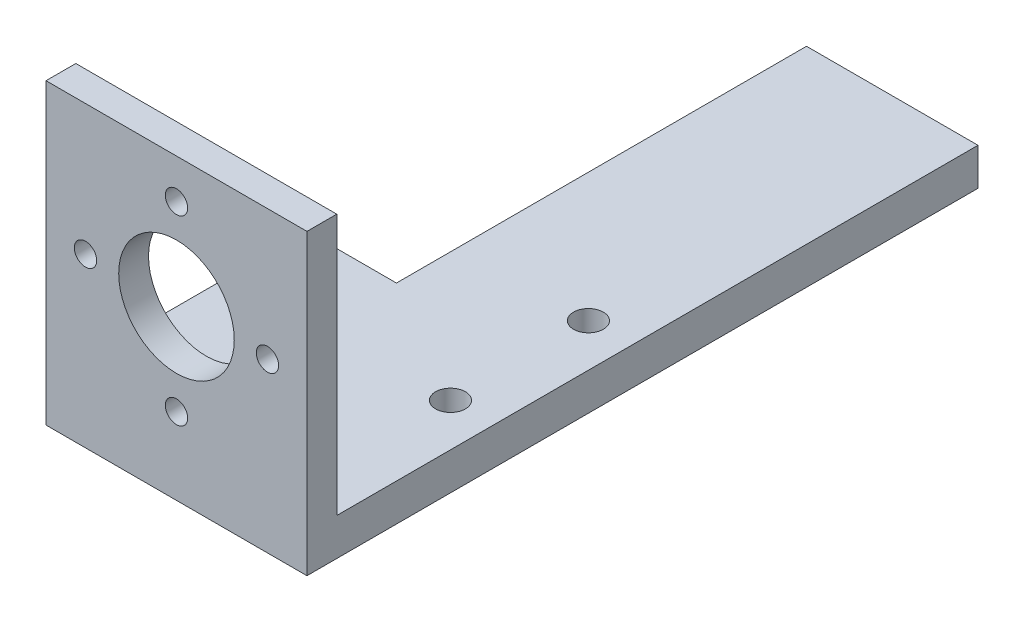
SolidWorks part; units mm, degrees
ref_plane "Front Plane" through (0, 0, 0) normal (0, 0, 1) x (1, 0, 0)
ref_plane "Top Plane" through (0, 0, 0) normal (0, 1, 0) x (1, 0, 0)
ref_plane "Right Plane" through (0, 0, 0) normal (1, 0, 0) x (0, 0, -1)
sketch "Sketch1" plane through (0, 0, 0) normal (0, 1, 0) x (1, 0, 0)
  line L0 (-17.5, 45) -> (17.5, 45)
  line L1 (17.5, 45) -> (17.5, -45)
  line L2 (17.5, -45) -> (-17.5, -45)
  line L3 (-17.5, -45) -> (-17.5, 45)
  line L4 (-11.75, -20) -> (11.75, -20)
  line L5 (-17.5, -10) -> (-5.5, -10)
  line L6 (-5.5, -10) -> (-5.5, 45)
  circle A0 centre (-11.75, -20) radius 2
  circle A1 centre (11.75, -20) radius 2
  circle A2 centre (11.75, -1.5) radius 2
  point P2 (-17.5, 0)
  point P5 (0, -45)
  point P9 (0, -20)
  point P14 (0, 0)
  dimension "D4" = 4
  dimension "D1" = 35
  dimension "D2" = 90
  dimension "D3" = 23.5
  dimension "D5" = 18.5
  dimension "D6" = 25
  dimension "D7" = 35
  dimension "D8" = 12
extrude "Boss-Extrude1" add sketch "Sketch1" along normal mid plane 5
sketch "Sketch2" plane through (0, 2.5, 0) normal (0, 1, 0) x (1, 0, 0)
  line L0 (-17.5, -45) -> (17.5, -45)
  line L1 (17.5, -45) -> (17.5, -41)
  line L2 (17.5, 45) -> (17.5, -45) construction
  line L3 (17.5, -41) -> (-17.5, -41)
  line L4 (-17.5, -45) -> (-17.5, -10) construction
  line L5 (-17.5, -41) -> (-17.5, -45)
  dimension "D1" = 4
extrude "Boss-Extrude2" add sketch "Sketch2" along normal blind 35
sketch "Sketch3" plane through (0, 0, 41) normal (0, 0, -1) x (-1, 0, 0)
  line L0 (0, 7.8) -> (0, 32.2)
  line L1 (17.5, 37.5) -> (17.5, 2.5) construction
  line L2 (12.2, 20) -> (-12.2, 20)
  circle A0 centre (-12.2, 20) radius 1.5
  circle A1 centre (0, 7.8) radius 1.5
  circle A2 centre (12.2, 20) radius 1.5
  circle A3 centre (0, 32.2) radius 1.5
  circle A4 centre (0, 20) radius 7.75
  point P3 (0, 20)
  point P6 (17.5, 20)
  point P9 (0, 20)
  dimension "D3" = 3
  dimension "D4" = 15.5
  dimension "D1" = 24.4
  dimension "D2" = 24.4
extrude "Cut-Extrude1" cut sketch "Sketch3" against normal up to next
